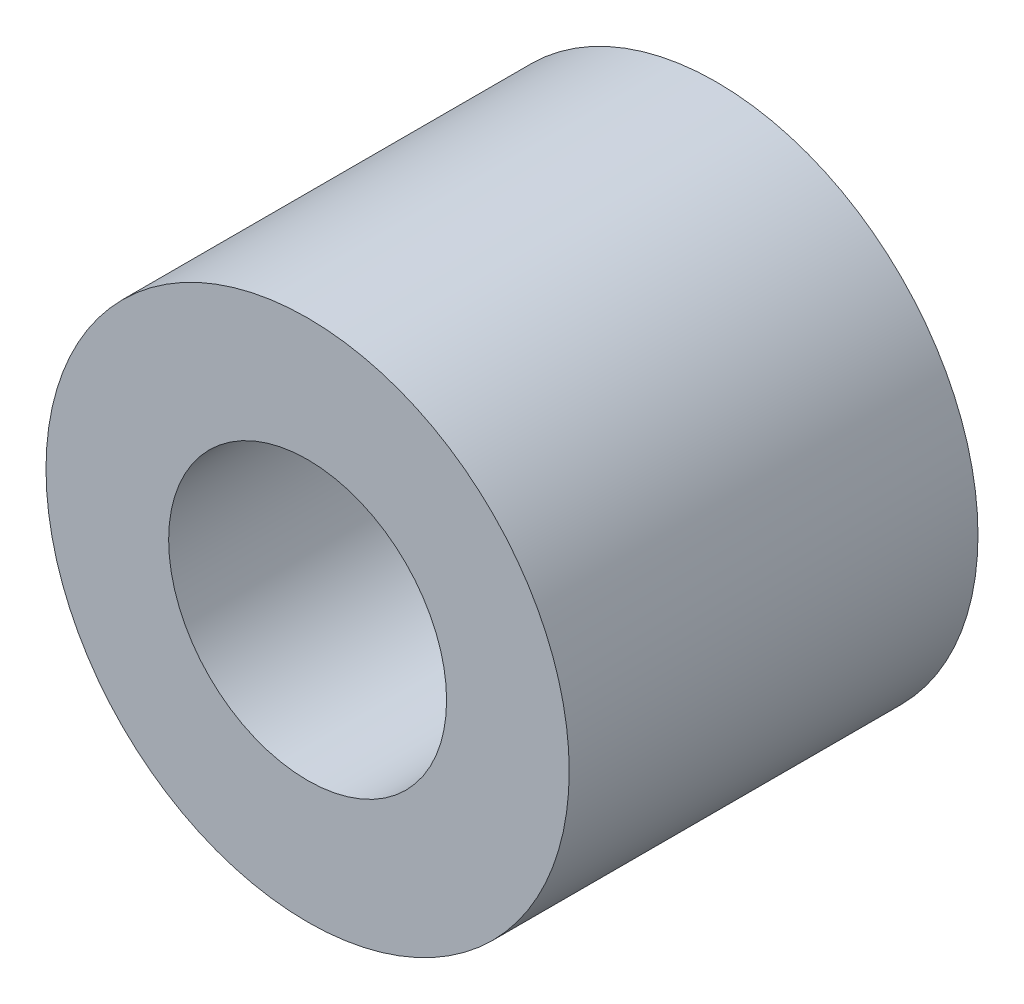
SolidWorks part; units mm, degrees
material "Nylon 101"
ref_plane "Plan de face" through (0, 0, 0) normal (0, 0, 1) x (1, 0, 0)
ref_plane "Plan de dessus" through (0, 0, 0) normal (0, 1, 0) x (1, 0, 0)
ref_plane "Plan de droite" through (0, 0, 0) normal (1, 0, 0) x (0, 0, -1)
sketch "Esquisse1" plane through (0, 0, 0) normal (0, 0, 1) x (1, 0, 0)
  circle A0 centre (-30.3019, 53.6) radius 3.2
  circle A1 centre (-30.3019, 53.6) radius 1.7
  dimension "D1" = 3.4
  dimension "D2" = 1.5
extrude "Boss.-Extru.1" add sketch "Esquisse1" along normal blind 5 contours A0
